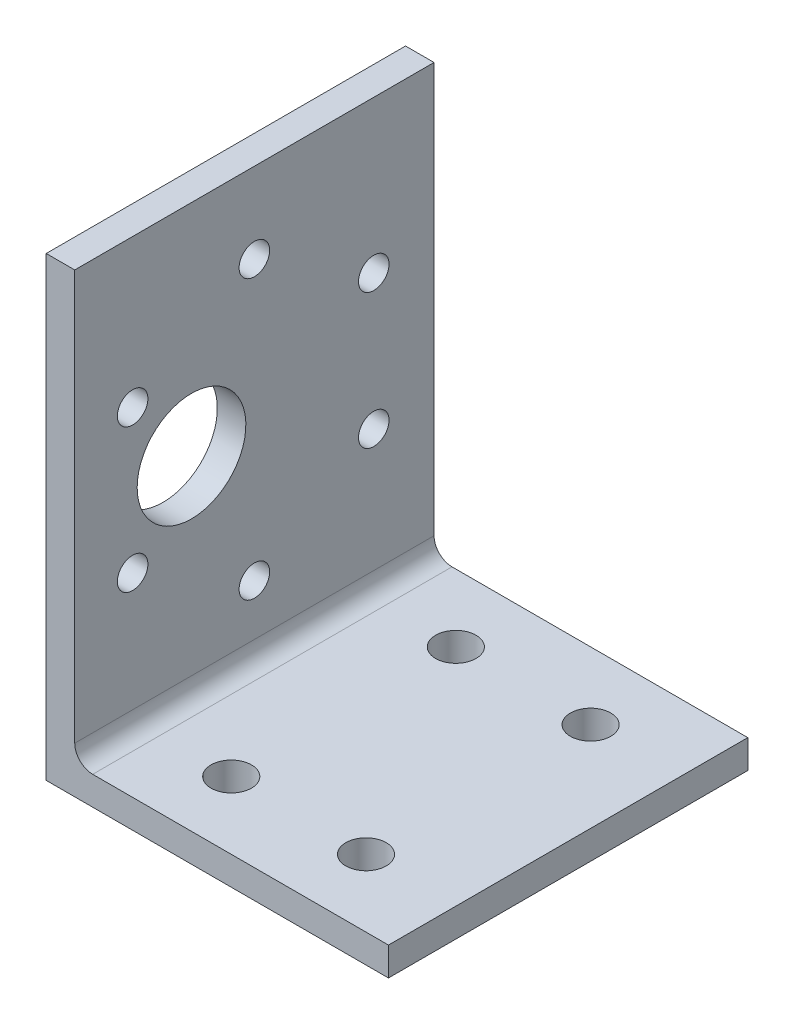
SolidWorks part; units mm, degrees
material "6061-T6 (SS)"
ref_plane "Front Plane" through (0, 0, 0) normal (0, 0, 1) x (1, 0, 0)
ref_plane "Top Plane" through (0, 0, 0) normal (0, 1, 0) x (1, 0, 0)
ref_plane "Right Plane" through (0, 0, 0) normal (1, 0, 0) x (0, 0, -1)
sketch "Sketch1" plane through (0, 0, 0) normal (0, 0, 1) x (1, 0, 0)
  line L0 (0, 0) -> (0, 50.8)
  line L1 (0, 50.8) -> (3.175, 50.8)
  line L2 (3.175, 50.8) -> (3.175, 3.175)
  line L3 (3.175, 3.175) -> (38.1, 3.175)
  line L4 (38.1, 3.175) -> (38.1, 0)
  line L5 (38.1, 0) -> (0, 0)
  dimension "D1" = 3.175
  dimension "D2" = 3.175
  dimension "D3" = 38.1
  dimension "D4" = 50.8
extrude "Boss-Extrude1" add sketch "Sketch1" along normal mid plane 40
fillet "Fillet1" radius 2 1 edges at (3.175, 3.175, 0)
sketch "Sketch10" plane through (0, 0, 0) normal (-1, 0, 0) x (0, 0, 1)
  line L0 (20, 0) -> (-20, 0) construction
  circle A0 centre (0.2647, 26.35) radius 15.5
  point P0 (0, 41.8477)
  point P2 (13.5538, 34.3281)
  point P4 (-13.2891, 18.8304)
  point P6 (0, 10.8523)
  point P17 (-13.2891, 33.8696)
  point P19 (13.5538, 18.3719)
  dimension "D1" = 31
  dimension "D2" = 60
  dimension "D3" = 60
  dimension "D4" = 26.35
hole_wizard "M3 Clearance Hole1" positions "Sketch10" profile "Sketch3" hole size "M3" standard "ANSI Metric" end condition through all
sketch "Sketch3" plane through (0, 41.8477, 0) normal (0, 1, 0) x (0, 0, 1)
  line L0 (0, 0) -> (0, 38.1)
  line L1 (0, 38.1) -> (1.7, 38.1)
  line L2 (1.7, 38.1) -> (1.7, 0)
  line L5 (1.7, 0) -> (0, 0)
  line L11 (0, -6.35) -> (0, 107.95) construction
  dimension "Thru Hole Dia." = 3.4
  dimension "Thru Hole Depth" = 38.1
sketch "Sketch6" plane through (0, 0, 0) normal (-1, 0, 0) x (0, 0, 1)
  line L0 (20, 0) -> (-20, 0) construction
  circle A0 centre (7, 26.35) radius 6.05
  circle A3 centre (0, 41.8477) radius 1.7 construction
  dimension "D2" = 12.1
  dimension "D1" = 26.35
  dimension "D3" = 7
extrude "Cut-Extrude1" cut sketch "Sketch6" against normal through all
hole_wizard "M4 Clearance Hole1" positions "Sketch14" profile "Sketch12" hole size "M4" standard "ANSI Metric" end condition through all
sketch "Sketch14" plane through (0, 3.175, 0) normal (0, 1, 0) x (1, 0, 0)
  line L0 (38.1, 20) -> (5.175, 20) construction
  line L1 (38.1, -20) -> (38.1, 20) construction
  point P0 (13.1, -12.5)
  point P2 (28.1, -12.5)
  point P4 (28.1, 12.5)
  point P6 (13.1, 12.5)
  dimension "D1" = 15
  dimension "D2" = 25
  dimension "D3" = 7.5
  dimension "D4" = 10
sketch "Sketch12" plane through (13.1, 3.175, 12.5) normal (1, 0, 0) x (0, 0, 1)
  line L0 (0, 0) -> (0, 3.175)
  line L1 (0, 3.175) -> (2.25, 3.175)
  line L2 (2.25, 3.175) -> (2.25, 0)
  line L5 (2.25, 0) -> (0, 0)
  line L11 (0, -6.35) -> (0, 107.95) construction
  dimension "Thru Hole Dia." = 4.5
  dimension "Thru Hole Depth" = 3.175
